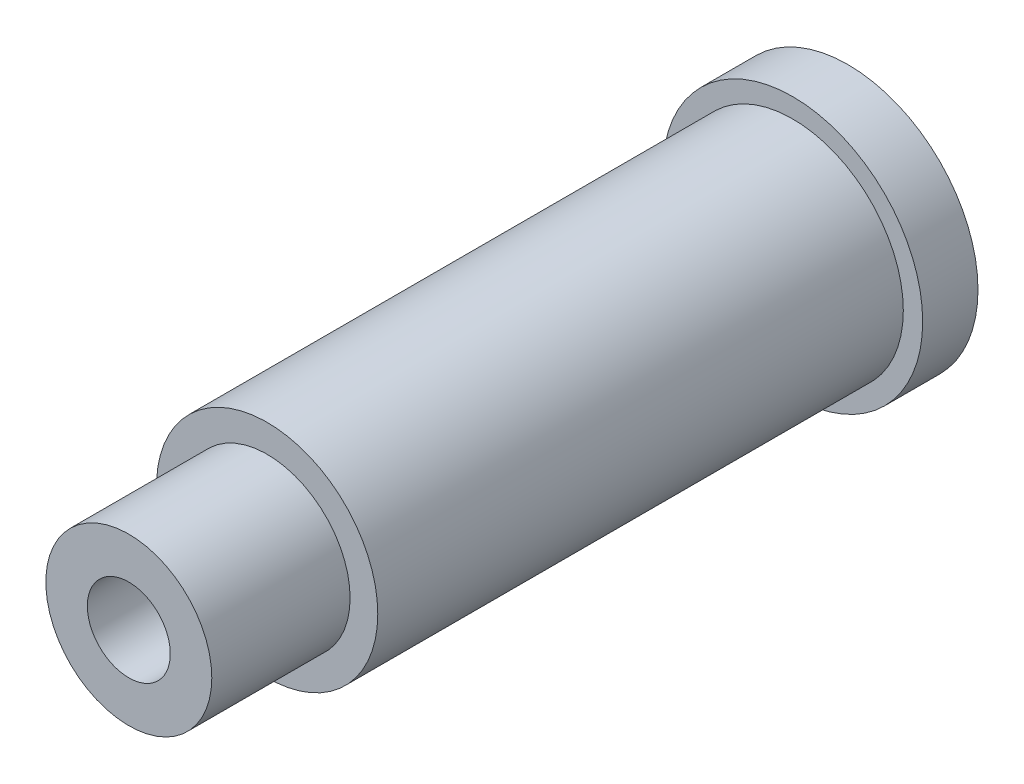
SolidWorks part; units mm, degrees
ref_plane "Front" through (0, 0, 0) normal (0, 0, 1) x (1, 0, 0)
ref_plane "Top" through (0, 0, 0) normal (0, 1, 0) x (1, 0, 0)
ref_plane "Right" through (0, 0, 0) normal (1, 0, 0) x (0, 0, -1)
sketch "Sketch1" plane through (0, 0, 0) normal (0, 0, 1) x (1, 0, 0)
  circle A0 centre (0, 0) radius 4.7
extrude "Extrude1" add sketch "Sketch1" along normal blind 2
sketch "Sketch2" plane through (0, 0, 2) normal (0, 0, 1) x (1, 0, 0)
  circle A0 centre (0, 0) radius 4
extrude "Extrude2" add sketch "Sketch2" along normal blind 19
sketch "Sketch3" plane through (0, 0, 21) normal (0, 0, 1) x (1, 0, 0)
  circle A0 centre (0, 0) radius 3
extrude "Extrude3" add sketch "Sketch3" along normal blind 5
sketch "Sketch4" plane through (0, 0, 0) normal (0, 0, -1) x (-1, 0, 0)
  circle A0 centre (0, 0) radius 1.5
extrude "Cut-Extrude1" cut sketch "Sketch4" against normal through all
